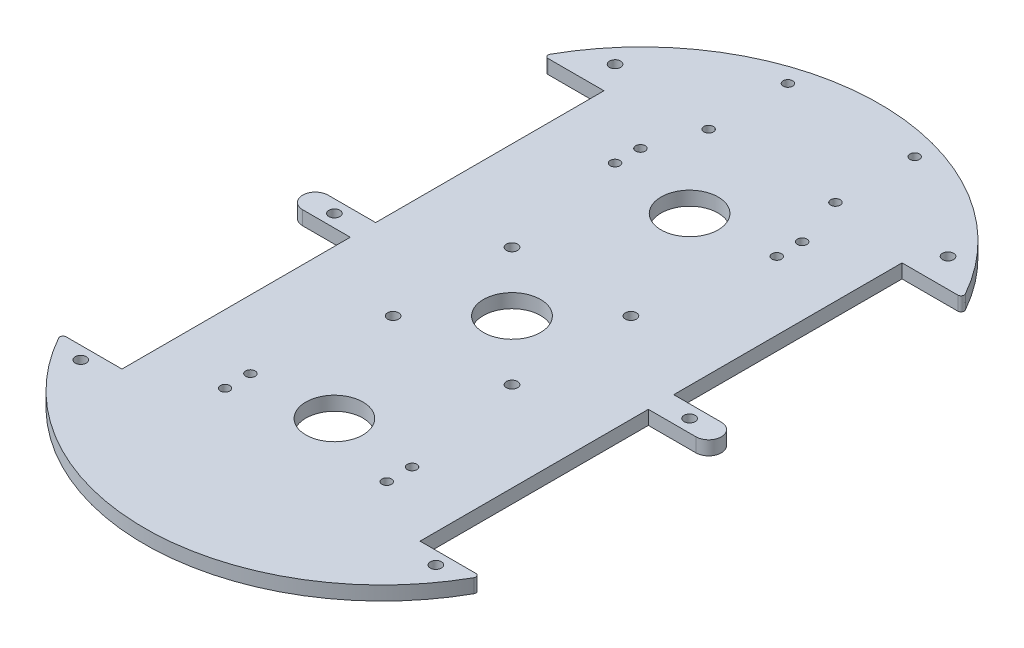
SolidWorks part; units mm, degrees
material "ABS PC"
ref_plane "Front Plane" through (0, 0, 0) normal (0, 0, 1) x (1, 0, 0)
ref_plane "Top Plane" through (0, 0, 0) normal (0, 1, 0) x (1, 0, 0)
ref_plane "Right Plane" through (0, 0, 0) normal (1, 0, 0) x (0, 0, -1)
ref_plane "Plane1" through (0, 4.4, 0) normal (0, 1, 0) x (1, 0, 0)
sketch "Sketch2" plane through (0, 0, 0) normal (0, 1, 0) x (1, 0, 0)
  line L1 (-66, 116) -> (66, 116)
  line L2 (-66, 116) -> (-66, -116)
  line L3 (-66, -116) -> (66, -116)
  line L4 (66, 116) -> (66, -116)
  point P4 (66, 0)
  point P6 (0, 116)
  dimension "D1" = 132
  dimension "D2" = 232
extrude "Plate Size" add sketch "Sketch2" along normal up to surface (8.8 mm away)
sketch "Sketch4" plane through (0, 0, 0) normal (0, 1, 0) x (1, 0, 0)
  line L0 (-66, 116) -> (-66, -116) construction
  line L1 (66, 116) -> (66, -116) construction
  line L2 (0, -40.9051) -> (0, 40.9051) construction
  line L4 (-64.6, 76) -> (-47, 76)
  line L6 (-62, 4) -> (-47, 4)
  line L7 (-47, 76) -> (-47, 4)
  line L8 (-47, -4) -> (-47, 4) construction
  line L9 (64.6, 76) -> (47, 76)
  line L11 (62, 4) -> (47, 4)
  line L12 (47, 76) -> (47, 4)
  line L13 (64.6, -76) -> (47, -76)
  line L15 (62, -4) -> (47, -4)
  line L16 (47, -76) -> (47, -4)
  line L17 (-47, -76) -> (-64.6, -76)
  line L18 (-47, -76) -> (-47, -4)
  line L19 (-47, -4) -> (-62, -4)
  line L21 (47, -4) -> (47, 4) construction
  line L23 (-47, 40) -> (47, 40) construction
  line L24 (0, -2.475) -> (0, 2.475) construction
  arc A0 (65.473, 77.4878) -> (-65.473, 77.4878) centre (0, 40.9051) ccw
  arc A1 (-65.473, -77.4878) -> (65.473, -77.4878) centre (0, -40.9051) ccw
  arc A2 (-62, 4) -> (-62, -4) centre (-62, 0) ccw
  arc A3 (62, -4) -> (62, 4) centre (62, 0) ccw
  arc A4 (-64.6, -76) -> (-65.473, -77.4878) centre (-64.6, -77) ccw
  arc A5 (65.473, -77.4878) -> (64.6, -76) centre (64.6, -77) ccw
  arc A6 (64.6, 76) -> (65.473, 77.4878) centre (64.6, 77) ccw
  arc A7 (-65.473, 77.4878) -> (-64.6, 76) centre (-64.6, 77) ccw
  point P2 (0, 0)
  point P33 (-47, 0)
  point P39 (0, 40)
  dimension "D1" = 150
  dimension "D2" = 231.8102
  dimension "D6" = 2
  dimension "D3" = 72
  dimension "D4" = 8
  dimension "D5" = 94
extrude "Outer Profile" cut sketch "Sketch4" along normal through all flip side to cut
hole_wizard "M3 Clearance Hole1" positions "Sketch5" profile "Sketch6" hole size "M3" standard "ANSI Metric" end condition through all
sketch "Sketch5" plane through (0, 0, 0) normal (0, 1, 0) x (1, 0, 0)
  line L1 (-56, -80) -> (56, -80) construction
  line L5 (0, -2.42) -> (0, 2.42) construction
  line L7 (-2.42, 0) -> (2.42, 0) construction
  line L8 (-52.5, 85) -> (52.5, 85) construction
  line L10 (56, 0) -> (-56, 0) construction
  circle A0 centre (-56, -80) radius 1.75 construction
  point P0 (-56, -80)
  point P159 (56, -80)
  point P161 (0, -80)
  point P171 (-52.5, 85)
  point P177 (52.5, 85)
  point P179 (0, 85)
  point P184 (-56, 0)
  point P186 (56, 0)
  point P192 (0, 0)
  dimension "D1" = 80
  dimension "D3" = 3.5
  dimension "D2" = 56
  dimension "D4" = 52.5
  dimension "D5" = 85
sketch "Sketch6" plane through (-56, 0, 80) normal (1, 0, 0) x (0, 0, -1)
  line L0 (0, 0) -> (0, 4.4)
  line L1 (0, 4.4) -> (1.75, 4.4)
  line L2 (1.75, 4.4) -> (1.75, 0)
  line L5 (1.75, 0) -> (0, 0)
  line L11 (0, -6.35) -> (0, 107.95) construction
  dimension "Thru Hole Dia." = 3.5
  dimension "Thru Hole Depth" = 4.4
hole_wizard "Ø18.0 (18) Diameter Hole4" positions "Sketch9" profile "Sketch10" hole size "Ø18.0" standard "ANSI Metric" end condition through all
sketch "Sketch9" plane through (0, 0, 0) normal (0, 1, 0) x (1, 0, 0)
  line L0 (0, -2.42) -> (0, 2.42) construction
  line L1 (0, -56) -> (0, 56) construction
  line L3 (-2.42, 0) -> (2.42, 0) construction
  point P0 (0, 56)
  point P2 (0, -56)
  point P10 (0, 0)
  dimension "D1" = 56
sketch "Sketch10" plane through (0, 0, -56) normal (1, 0, 0) x (0, 0, -1)
  line L0 (0, 0) -> (0, 4.4)
  line L1 (0, 4.4) -> (9, 4.4)
  line L2 (9, 4.4) -> (9, 0)
  line L5 (9, 0) -> (0, 0)
  line L11 (0, -6.35) -> (0, 107.95) construction
  dimension "Thru Hole Dia." = 18
  dimension "Thru Hole Depth" = 4.4
hole_wizard "M3 Clearance Hole2" positions "Sketch11" profile "Sketch12" hole size "M3" standard "ANSI Metric" end condition through all
sketch "Sketch11" plane through (0, 0, 0) normal (0, 1, 0) x (1, 0, 0)
  line L1 (18.75, 18.75) -> (-18.75, 18.75) construction
  line L2 (18.75, 18.75) -> (18.75, -18.75) construction
  line L3 (18.75, -18.75) -> (-18.75, -18.75) construction
  line L4 (-18.75, 18.75) -> (-18.75, -18.75) construction
  line L5 (0, -2.42) -> (0, 2.42) construction
  line L6 (-2.42, 0) -> (2.42, 0) construction
  point P0 (18.75, 18.75)
  point P4 (-18.75, -18.75)
  point P31 (18.75, -18.75)
  point P32 (-18.75, 18.75)
  point P39 (0, 18.75)
  point P42 (18.75, 0)
  dimension "D1" = 37.5
sketch "Sketch12" plane through (18.75, 0, -18.75) normal (1, 0, 0) x (0, 0, -1)
  line L0 (0, 0) -> (0, 4.4)
  line L1 (0, 4.4) -> (1.75, 4.4)
  line L2 (1.75, 4.4) -> (1.75, 0)
  line L5 (1.75, 0) -> (0, 0)
  line L11 (0, -6.35) -> (0, 107.95) construction
  dimension "Thru Hole Dia." = 3.5
  dimension "Thru Hole Depth" = 4.4
hole_wizard "M3 Clearance Hole3" positions "Sketch13" profile "Sketch14" hole size "M3" standard "ANSI Metric" end condition through all
sketch "Sketch13" plane through (0, 0, 0) normal (0, 1, 0) x (1, 0, 0)
  line L1 (-25.5, 66) -> (25.5, 66) construction
  line L2 (-25.5, 66) -> (-25.5, -65) construction
  line L3 (-25.5, -65) -> (25.5, -65) construction
  line L4 (25.5, 66) -> (25.5, -65) construction
  line L5 (0, -2.42) -> (0, 2.42) construction
  line L7 (25.5, -57) -> (25.5, -65) construction
  line L10 (-25.5, -65) -> (-25.5, -57) construction
  line L13 (-25.5, 66) -> (-25.5, 58) construction
  line L16 (25.5, 58) -> (25.5, 66) construction
  point P0 (-25.5, 66)
  point P4 (25.5, -65)
  point P125 (-25.5, -65)
  point P126 (25.5, 66)
  point P128 (0, 66)
  point P140 (-25.5, 58)
  point P142 (25.5, 58)
  point P144 (25.5, -57)
  point P146 (-25.5, -57)
  dimension "D1" = 51
  dimension "D2" = 131
  dimension "D3" = 8
  dimension "D4" = 65
sketch "Sketch14" plane through (-25.5, 0, -66) normal (1, 0, 0) x (0, 0, -1)
  line L0 (0, 0) -> (0, 4.4)
  line L1 (0, 4.4) -> (1.5, 4.4)
  line L2 (1.5, 4.4) -> (1.5, 0)
  line L5 (1.5, 0) -> (0, 0)
  line L11 (0, -6.35) -> (0, 107.95) construction
  dimension "Thru Hole Dia." = 3
  dimension "Thru Hole Depth" = 4.4
hole_wizard "M3 Clearance Hole4" positions "Sketch15" profile "Sketch16" hole size "M3" standard "ANSI Metric" end condition through all
sketch "Sketch15" plane through (0, 0, 0) normal (0, 1, 0) x (1, 0, 0)
  line L1 (-20, 107) -> (20, 107) construction
  line L2 (-20, 107) -> (-20, 82) construction
  line L3 (-20, 82) -> (20, 82) construction
  line L4 (20, 107) -> (20, 82) construction
  line L5 (0, -2.42) -> (0, 2.42) construction
  line L6 (-66, 116) -> (66, 116) construction
  point P0 (-20, 107)
  point P65 (0, 82)
  point P74 (20, 107)
  point P77 (-20, 82)
  point P80 (20, 82)
  dimension "D1" = 40
  dimension "D2" = 25
  dimension "D3" = 9
sketch "Sketch16" plane through (-20, 0, -107) normal (1, 0, 0) x (0, 0, -1)
  line L0 (0, 0) -> (0, 4.4)
  line L1 (0, 4.4) -> (1.5, 4.4)
  line L2 (1.5, 4.4) -> (1.5, 0)
  line L5 (1.5, 0) -> (0, 0)
  line L11 (0, -6.35) -> (0, 107.95) construction
  dimension "Thru Hole Dia." = 3
  dimension "Thru Hole Depth" = 4.4
sketch "Sketch17" plane through (0, 4.4, 0) normal (0, 1, 0) x (1, 0, 0)
  circle A0 centre (0, 0) radius 9.017
  dimension "D1" = 18.034
extrude "Cut-Extrude1" cut sketch "Sketch17" against normal blind 53.34
